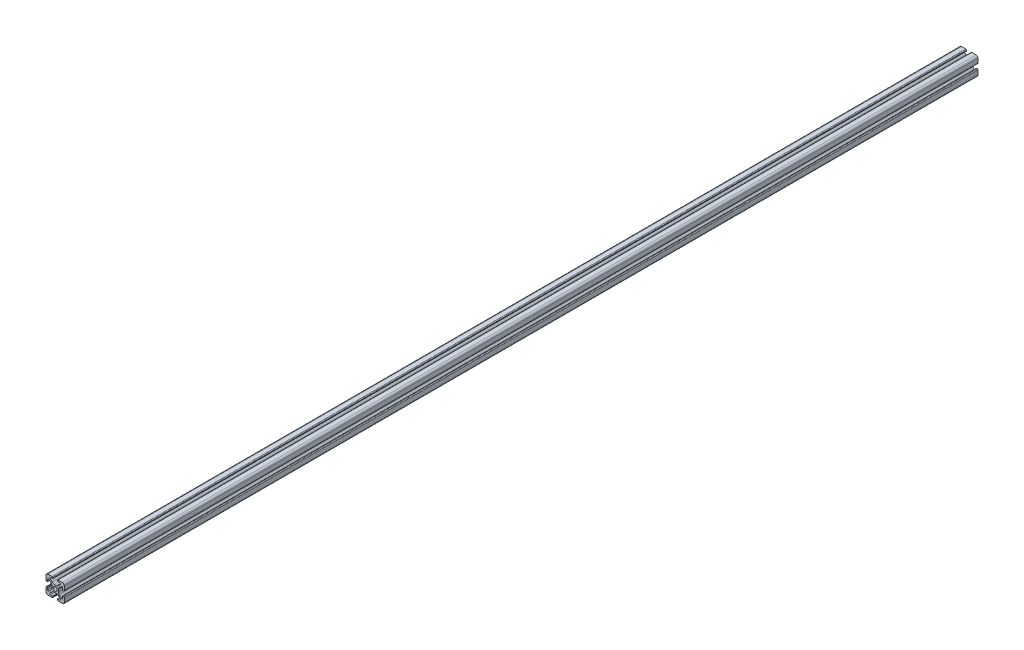
SolidWorks part; units mm, degrees
material "6061 Alloy"
ref_plane "Front Plane" through (0, 0, 0) normal (0, 0, 1) x (1, 0, 0)
ref_plane "Top Plane" through (0, 0, 0) normal (0, 1, 0) x (1, 0, 0)
ref_plane "Right Plane" through (0, 0, 0) normal (1, 0, 0) x (0, 0, -1)
sketch "Sketch1" plane through (0, 0, 0) normal (0, 0, 1) x (1, 0, 0)
  line L2 (-9.9949, 7.9883) -> (-9.9949, 3.2893)
  line L3 (-7.9883, 9.9949) -> (-3.2893, 9.9949)
  line L4 (-2.5019, 9.2075) -> (-2.5019, 8.4963)
  line L5 (-2.8067, 8.1915) -> (-4.9149, 8.1915)
  line L6 (-5.5076, 6.7606) -> (-3.2528, 4.5058)
  line L7 (-6.7606, 5.5076) -> (-4.5058, 3.2528)
  line L8 (-8.1915, 4.9149) -> (-8.1915, 2.8067)
  line L9 (-8.4963, 2.5019) -> (-9.2075, 2.5019)
  line L11 (-1.1334, 3.6279) -> (1.1334, 3.6279)
  line L12 (-3.6279, 1.1334) -> (-3.6279, -1.1334)
  line L13 (8.4963, 2.5019) -> (9.2075, 2.5019)
  line L14 (8.1915, 4.9149) -> (8.1915, 2.8067)
  line L15 (9.9949, 7.9883) -> (9.9949, 3.2893)
  line L16 (7.9883, 9.9949) -> (3.2893, 9.9949)
  line L17 (2.5019, 9.2075) -> (2.5019, 8.4963)
  line L18 (2.8067, 8.1915) -> (4.9149, 8.1915)
  line L19 (3.6279, 1.1334) -> (3.6279, -1.1334)
  line L20 (5.5076, 6.7606) -> (3.2528, 4.5058)
  line L21 (6.7606, 5.5076) -> (4.5058, 3.2528)
  line L22 (-8.4963, -2.5019) -> (-9.2075, -2.5019)
  line L23 (-8.1915, -4.9149) -> (-8.1915, -2.8067)
  line L24 (-6.7606, -5.5076) -> (-4.5058, -3.2528)
  line L25 (-5.5076, -6.7606) -> (-3.2528, -4.5058)
  line L26 (-2.8067, -8.1915) -> (-4.9149, -8.1915)
  line L27 (-2.5019, -9.2075) -> (-2.5019, -8.4963)
  line L28 (-7.9883, -9.9949) -> (-3.2893, -9.9949)
  line L29 (-9.9949, -7.9883) -> (-9.9949, -3.2893)
  line L30 (9.9949, -7.9883) -> (9.9949, -3.2893)
  line L31 (7.9883, -9.9949) -> (3.2893, -9.9949)
  line L32 (2.5019, -9.2075) -> (2.5019, -8.4963)
  line L33 (2.8067, -8.1915) -> (4.9149, -8.1915)
  line L34 (5.5076, -6.7606) -> (3.2528, -4.5058)
  line L35 (6.7606, -5.5076) -> (4.5058, -3.2528)
  line L36 (8.1915, -4.9149) -> (8.1915, -2.8067)
  line L37 (8.4963, -2.5019) -> (9.2075, -2.5019)
  line L38 (-1.1334, -3.6279) -> (1.1334, -3.6279)
  circle A0 centre (0, 0) radius 2.1463
  arc A1 (-9.9949, 7.9883) -> (-7.9883, 9.9949) centre (-7.9883, 7.9883) cw
  arc A2 (-6.7606, 5.5076) -> (-8.1915, 4.9149) centre (-7.3533, 4.9149) ccw
  arc A3 (-4.9149, 8.1915) -> (-5.5076, 6.7606) centre (-4.9149, 7.3533) ccw
  arc A4 (-3.2893, 9.9949) -> (-2.5019, 9.2075) centre (-3.2893, 9.2075) cw
  arc A5 (-9.9949, 3.2893) -> (-9.2075, 2.5019) centre (-9.2075, 3.2893) ccw
  arc A6 (-8.1915, 2.8067) -> (-8.4963, 2.5019) centre (-8.4963, 2.8067) cw
  arc A7 (-2.5019, 8.4963) -> (-2.8067, 8.1915) centre (-2.8067, 8.4963) cw
  arc A8 (-1.1334, 3.6279) -> (-3.2528, 4.5058) centre (-1.1334, 6.6251) cw
  arc A9 (-3.6279, 1.1334) -> (-4.5058, 3.2528) centre (-6.6251, 1.1334) ccw
  arc A10 (8.1915, 2.8067) -> (8.4963, 2.5019) centre (8.4963, 2.8067) ccw
  arc A11 (9.9949, 3.2893) -> (9.2075, 2.5019) centre (9.2075, 3.2893) cw
  arc A12 (9.9949, 7.9883) -> (7.9883, 9.9949) centre (7.9883, 7.9883) ccw
  arc A13 (3.2893, 9.9949) -> (2.5019, 9.2075) centre (3.2893, 9.2075) ccw
  arc A14 (2.5019, 8.4963) -> (2.8067, 8.1915) centre (2.8067, 8.4963) ccw
  arc A15 (1.1334, 3.6279) -> (3.2528, 4.5058) centre (1.1334, 6.6251) ccw
  arc A16 (3.6279, 1.1334) -> (4.5058, 3.2528) centre (6.6251, 1.1334) cw
  arc A17 (6.7606, 5.5076) -> (8.1915, 4.9149) centre (7.3533, 4.9149) cw
  arc A18 (4.9149, 8.1915) -> (5.5076, 6.7606) centre (4.9149, 7.3533) cw
  arc A19 (-3.6279, -1.1334) -> (-4.5058, -3.2528) centre (-6.6251, -1.1334) cw
  arc A20 (-1.1334, -3.6279) -> (-3.2528, -4.5058) centre (-1.1334, -6.6251) ccw
  arc A21 (-2.5019, -8.4963) -> (-2.8067, -8.1915) centre (-2.8067, -8.4963) ccw
  arc A22 (-8.1915, -2.8067) -> (-8.4963, -2.5019) centre (-8.4963, -2.8067) ccw
  arc A23 (-9.9949, -3.2893) -> (-9.2075, -2.5019) centre (-9.2075, -3.2893) cw
  arc A24 (-3.2893, -9.9949) -> (-2.5019, -9.2075) centre (-3.2893, -9.2075) ccw
  arc A25 (-4.9149, -8.1915) -> (-5.5076, -6.7606) centre (-4.9149, -7.3533) cw
  arc A26 (-6.7606, -5.5076) -> (-8.1915, -4.9149) centre (-7.3533, -4.9149) cw
  arc A27 (-9.9949, -7.9883) -> (-7.9883, -9.9949) centre (-7.9883, -7.9883) ccw
  arc A28 (9.9949, -7.9883) -> (7.9883, -9.9949) centre (7.9883, -7.9883) cw
  arc A29 (6.7606, -5.5076) -> (8.1915, -4.9149) centre (7.3533, -4.9149) ccw
  arc A30 (4.9149, -8.1915) -> (5.5076, -6.7606) centre (4.9149, -7.3533) ccw
  arc A31 (3.2893, -9.9949) -> (2.5019, -9.2075) centre (3.2893, -9.2075) cw
  arc A32 (9.9949, -3.2893) -> (9.2075, -2.5019) centre (9.2075, -3.2893) ccw
  arc A33 (8.1915, -2.8067) -> (8.4963, -2.5019) centre (8.4963, -2.8067) cw
  arc A34 (2.5019, -8.4963) -> (2.8067, -8.1915) centre (2.8067, -8.4963) cw
  arc A35 (1.1334, -3.6279) -> (3.2528, -4.5058) centre (1.1334, -6.6251) cw
  arc A36 (3.6279, -1.1334) -> (4.5058, -3.2528) centre (6.6251, -1.1334) ccw
extrude "Boss-Extrude1" add sketch "Sketch1" along normal mid plane 1000.125
